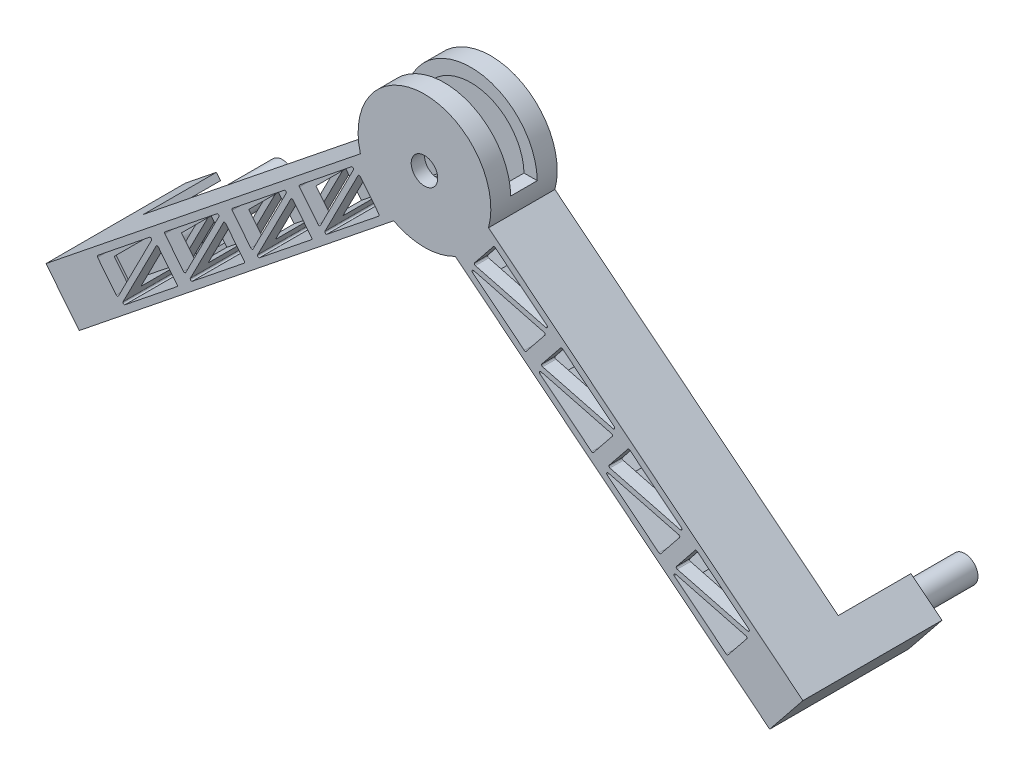
SolidWorks part; units mm, degrees
other "Markup1"
sketch "Sketch10" plane through (-187.1162, -34.3281, 104.7573) normal (-0.0779, -0.0282, 0.9966) x (0.967, 0.2412, 0.0824)
other "Markup2"
sketch "Sketch11" plane through (-187.1162, -34.3281, 104.7573) normal (-0.0779, -0.0282, 0.9966) x (0.967, 0.2412, 0.0824)
material "1060 Alloy"
ref_plane "Front Plane" through (0, 0, 0) normal (0, 0, 1) x (1, 0, 0)
ref_plane "Top Plane" through (0, 0, 0) normal (0, 1, 0) x (1, 0, 0)
ref_plane "Right Plane" through (0, 0, 0) normal (1, 0, 0) x (0, 0, -1)
sketch "Sketch1" plane through (0, 0, 0) normal (0, 0, 1) x (1, 0, 0)
  line L0 (-187.1162, 0) -> (375.3401, 0) construction
  line L1 (-187.1162, 0) -> (45.8528, 186.9213)
  line L2 (142.3711, 186.9213) -> (375.3401, 0)
  line L3 (-187.1162, 0) -> (-162.0839, -31.199)
  line L4 (-162.0839, -31.199) -> (70.8851, 155.7223)
  line L5 (117.3388, 155.7223) -> (350.3077, -31.199)
  line L6 (350.3077, -31.199) -> (375.3401, 0)
  arc A0 (70.8851, 155.7223) -> (117.3388, 155.7223) centre (94.1119, 200) ccw
  arc A1 (142.3711, 186.9213) -> (45.8528, 186.9213) centre (94.1119, 200) ccw
  dimension "D4" = 100
  dimension "D1" = 200
  dimension "D3" = 40
extrude "Boss-Extrude1" add sketch "Sketch1" along normal blind 50
shell "Shell1" thickness 10
sketch "Sketch2" plane through (0, 0, 50) normal (0, 0, 1) x (1, 0, 0)
  circle A0 centre (94.1119, 200) radius 10
  dimension "D1" = 20
extrude "Cut-Extrude1" cut sketch "Sketch2" against normal blind 50
ref_plane "Plane1" through (0, 251, 0) normal (0, 1, 0) x (1, 0, 0)
sketch "Sketch5" plane through (0, 251, 0) normal (0, 1, 0) x (1, 0, 0)
  line L0 (44.1119, 0) -> (44.1119, -50) construction
  line L1 (44.1119, -15) -> (144.1119, -15)
  line L2 (44.1119, -15) -> (44.1119, -35)
  line L3 (44.1119, -35) -> (144.1119, -35)
  line L4 (144.1119, -15) -> (144.1119, -35)
  line L5 (144.1119, -50) -> (144.1119, 0) construction
  line L6 (144.1119, 0) -> (44.1119, 0) construction
  dimension "D1" = 20
  dimension "D2" = 15
extrude "Cut-Extrude2" cut sketch "Sketch5" against normal blind 50
sketch "Sketch6" plane through (228.3429, -183.2096, 0) normal (0.78, -0.6258, 0) x (0, 0, -1)
  line L0 (-50, 234.8913) -> (0, 234.8913) construction
  line L1 (-40, 224.8913) -> (-10, 224.8913)
  line L2 (-40, 224.8913) -> (-40, 204.8913)
  line L3 (-40, 204.8913) -> (-10, 204.8913)
  line L4 (-10, 224.8913) -> (-10, 204.8913)
  line L5 (-50, 194.8913) -> (0, 194.8913) construction
  line L6 (0, 194.8913) -> (0, 234.8913) construction
  line L7 (-50, 194.8913) -> (-50, 234.8913) construction
  dimension "D1" = 10
  dimension "D2" = 10
  dimension "D3" = 10
  dimension "D4" = 10
extrude "Cut-Extrude3" cut sketch "Sketch6" against normal blind 50
sketch "Sketch7" plane through (228.3429, -183.2096, 0) normal (0.78, -0.6258, 0) x (0, 0, -1)
  line L0 (-50, 194.8913) -> (0, 194.8913) construction
  line L1 (0, 234.8913) -> (-4.7573, 234.8913)
  line L2 (0, 234.8913) -> (0, 194.8913)
  line L3 (0, 194.8913) -> (-4.7573, 194.8913)
  line L4 (-4.7573, 234.8913) -> (-4.7573, 194.8913)
extrude "Boss-Extrude2" add sketch "Sketch7" along normal blind 5
sketch "Sketch8" plane through (0, 0, 4.7573) normal (0, 0, 1) x (1, 0, 0)
  line L4 (375.3401, 0) -> (350.3077, -31.199)
  line L5 (350.3077, -31.199) -> (354.2076, -34.3281)
  line L6 (354.2076, -34.3281) -> (379.24, -3.129)
  line L7 (379.24, -3.129) -> (375.3401, 0)
  line L8 (375.3401, 0) -> (350.3077, -31.199)
  line L9 (350.3077, -31.199) -> (354.2076, -34.3281)
  line L10 (354.2076, -34.3281) -> (379.24, -3.129)
  line L11 (379.24, -3.129) -> (375.3401, 0)
  dimension "D1" = 0
extrude "Boss-Extrude3" add sketch "Sketch8" along normal blind 100
sketch "Sketch9" plane through (0, 0, 50) normal (0, 0, 1) x (1, 0, 0)
  line L0 (375.3401, 0) -> (355.8407, 15.6452)
  line L1 (375.3401, 0) -> (142.3711, 186.9213) construction
  line L2 (355.8407, 15.6452) -> (352.7117, 11.7454)
  line L3 (352.7117, 11.7454) -> (372.2111, -3.8999)
  line L4 (375.3401, 0) -> (350.3077, -31.199) construction
  line L5 (372.2111, -3.8999) -> (375.3401, 0)
  line L6 (350.3077, -31.199) -> (330.8083, -15.5538)
  line L7 (117.3388, 155.7223) -> (350.3077, -31.199) construction
  line L8 (330.8083, -15.5538) -> (333.9374, -11.6539)
  line L9 (333.9374, -11.6539) -> (353.4368, -27.2992)
  line L10 (350.3077, -31.199) -> (375.3401, 0) construction
  line L11 (353.4368, -27.2992) -> (350.3077, -31.199)
  dimension "D1" = 5
  dimension "D2" = 25
extrude "Boss-Extrude4" add sketch "Sketch9" along normal up to surface (54.7573 mm away) up to face at (364.7739, -17.164, 104.7573)
sketch "Sketch12" plane through (-113.8345, -91.3345, 0) normal (-0.78, -0.6258, 0) x (0, 0, 1)
  line L0 (50, 77.0991) -> (0, 77.0991) construction
  line L1 (0, 117.0991) -> (9.973, 117.0991)
  line L2 (0, 117.0991) -> (0, 77.0991)
  line L3 (0, 77.0991) -> (9.973, 77.0991)
  line L4 (9.973, 117.0991) -> (9.973, 77.0991)
extrude "Boss-Extrude5" add sketch "Sketch12" along normal blind 5
sketch "Sketch13" plane through (0, 0, 9.973) normal (0, 0, 1) x (1, 0, 0)
  line L4 (-162.0839, -31.199) -> (-187.1162, 0)
  line L5 (-187.1162, 0) -> (-191.0161, -3.129)
  line L6 (-191.0161, -3.129) -> (-165.9837, -34.3281)
  line L7 (-165.9837, -34.3281) -> (-162.0839, -31.199)
  line L8 (-162.0839, -31.199) -> (-187.1162, 0)
  line L9 (-187.1162, 0) -> (-191.0161, -3.129)
  line L10 (-191.0161, -3.129) -> (-165.9837, -34.3281)
  line L11 (-165.9837, -34.3281) -> (-162.0839, -31.199)
  dimension "D1" = 0
extrude "Boss-Extrude6" add sketch "Sketch13" along normal blind 95
sketch "Sketch14" plane through (0, 0, 50) normal (0, 0, 1) x (1, 0, 0)
  line L0 (-187.1162, 0) -> (-167.6168, 15.6452)
  line L1 (45.8528, 186.9213) -> (-187.1162, 0) construction
  line L2 (-167.6168, 15.6452) -> (-164.4878, 11.7454)
  line L3 (-164.4878, 11.7454) -> (-183.9872, -3.8999)
  line L4 (-187.1162, 0) -> (-162.0839, -31.199) construction
  line L5 (-183.9872, -3.8999) -> (-187.1162, 0)
  line L6 (-162.0839, -31.199) -> (-165.2129, -27.2992)
  line L7 (-165.2129, -27.2992) -> (-145.7135, -11.6539)
  line L8 (-145.7135, -11.6539) -> (-142.5845, -15.5538)
  line L9 (-162.0839, -31.199) -> (70.8851, 155.7223) construction
  line L10 (-142.5845, -15.5538) -> (-162.0839, -31.199)
  dimension "D1" = 5
  dimension "D2" = 25
extrude "Boss-Extrude7" add sketch "Sketch14" along normal up to surface (54.973 mm away) up to face at (-176.55, -17.164, 104.973)
sketch "Sketch15" plane through (0, 0, 50) normal (0, 0, 1) x (1, 0, 0)
  line L0 (-152.1623, 20.3525) -> (-138.11, 2.8384)
  line L1 (-136.4396, 3.0091) -> (-111.4931, 51.8137)
  line L2 (-113.0094, 53.0488) -> (-152.0082, 21.7583)
  line L3 (-106.341, 50.0074) -> (-92.2886, 32.4933)
  line L4 (-92.4428, 31.0875) -> (-131.4416, -0.2029)
  line L5 (-132.9578, 1.0322) -> (-108.0114, 49.8368)
  line L6 (45.8528, 186.9213) -> (-167.6168, 15.6452) construction
  line L7 (-142.5845, -15.5538) -> (70.8851, 155.7223) construction
  line L8 (-183.9872, -3.8999) -> (-165.2129, -27.2992) construction
  line L9 (-62.3109, 93.7264) -> (-101.3097, 62.4359)
  line L10 (-101.4639, 61.0301) -> (-87.4115, 43.516)
  line L11 (-85.7411, 43.6867) -> (-60.7947, 92.4913)
  line L12 (-82.2594, 41.7098) -> (-57.3129, 90.5144)
  line L13 (-55.6425, 90.6851) -> (-41.5902, 73.1709)
  line L14 (-41.7443, 71.7651) -> (-80.7431, 40.4747)
  line L15 (-11.6125, 134.404) -> (-50.6113, 103.1135)
  line L16 (-50.7654, 101.7077) -> (-36.7131, 84.1936)
  line L17 (-35.0427, 84.3643) -> (-10.0962, 133.1689)
  line L18 (-31.5609, 82.3874) -> (-6.6145, 131.192)
  line L19 (-4.9441, 131.3627) -> (9.1083, 113.8485)
  line L20 (8.9541, 112.4428) -> (-30.0447, 81.1523)
  line L21 (39.086, 175.0816) -> (0.0872, 143.7911)
  line L22 (-0.067, 142.3853) -> (13.9854, 124.8712)
  line L23 (15.6558, 125.0419) -> (40.6022, 173.8465)
  line L24 (19.1375, 123.065) -> (44.084, 171.8696)
  line L25 (45.7544, 172.0403) -> (59.8067, 154.5261)
  line L26 (59.6526, 153.1204) -> (20.6538, 121.8299)
  line L27 (322.8636, -1.4868) -> (336.9159, 16.0273)
  line L28 (336.3873, 17.621) -> (283.3361, 31.3974)
  line L29 (282.459, 29.6495) -> (321.4578, -1.641)
  line L30 (338.4397, 23.1964) -> (299.4409, 54.4868)
  line L31 (298.0352, 54.3327) -> (283.9828, 36.8185)
  line L32 (284.5114, 35.2248) -> (337.5626, 21.4485)
  line L33 (117.3388, 155.7223) -> (330.8083, -15.5538) construction
  line L34 (355.8407, 15.6452) -> (142.3711, 186.9213) construction
  line L35 (353.4368, -27.2992) -> (372.2111, -3.8999) construction
  line L36 (233.8146, 75.9011) -> (286.8658, 62.1248)
  line L37 (287.7429, 63.8727) -> (248.7441, 95.1631)
  line L38 (247.3383, 95.009) -> (233.286, 77.4948)
  line L39 (231.7622, 70.3258) -> (270.761, 39.0353)
  line L40 (272.1667, 39.1895) -> (286.2191, 56.7036)
  line L41 (285.6905, 58.2973) -> (232.6393, 72.0737)
  line L42 (183.1178, 116.5774) -> (236.169, 102.8011)
  line L43 (237.0461, 104.5489) -> (198.0473, 135.8394)
  line L44 (196.6415, 135.6852) -> (182.5892, 118.1711)
  line L45 (181.0653, 111.0021) -> (220.0641, 79.7116)
  line L46 (221.4699, 79.8658) -> (235.5223, 97.3799)
  line L47 (234.9937, 98.9736) -> (181.9425, 112.75)
  line L48 (132.421, 157.2537) -> (185.4721, 143.4774)
  line L49 (186.3493, 145.2252) -> (147.3505, 176.5157)
  line L50 (145.9447, 176.3615) -> (131.8924, 158.8474)
  line L51 (130.3685, 151.6784) -> (169.3673, 120.3879)
  line L52 (170.7731, 120.5421) -> (184.8255, 138.0562)
  line L53 (184.2968, 139.6499) -> (131.2457, 153.4263)
  arc A0 (-152.1623, 20.3525) -> (-152.0082, 21.7583) centre (-151.3824, 20.9783) cw
  arc A1 (-136.4396, 3.0091) -> (-138.11, 2.8384) centre (-137.33, 3.4642) cw
  arc A2 (-111.4931, 51.8137) -> (-113.0094, 53.0488) centre (-112.3835, 52.2688) ccw
  arc A3 (-131.4416, -0.2029) -> (-132.9578, 1.0322) centre (-132.0674, 0.577) cw
  arc A4 (-92.4428, 31.0875) -> (-92.2886, 32.4933) centre (-93.0686, 31.8675) ccw
  arc A5 (-106.341, 50.0074) -> (-108.0114, 49.8368) centre (-107.1209, 49.3816) ccw
  arc A6 (-60.7947, 92.4913) -> (-62.3109, 93.7264) centre (-61.6851, 92.9464) ccw
  arc A7 (-101.4639, 61.0301) -> (-101.3097, 62.4359) centre (-100.6839, 61.6559) cw
  arc A8 (-85.7411, 43.6867) -> (-87.4115, 43.516) centre (-86.6316, 44.1418) cw
  arc A9 (-55.6425, 90.6851) -> (-57.3129, 90.5144) centre (-56.4225, 90.0592) ccw
  arc A10 (-80.7431, 40.4747) -> (-82.2594, 41.7098) centre (-81.3689, 41.2547) cw
  arc A11 (-41.7443, 71.7651) -> (-41.5902, 73.1709) centre (-42.3701, 72.5451) ccw
  arc A12 (-10.0962, 133.1689) -> (-11.6125, 134.404) centre (-10.9867, 133.624) ccw
  arc A13 (-50.7654, 101.7077) -> (-50.6113, 103.1135) centre (-49.9855, 102.3335) cw
  arc A14 (-35.0427, 84.3643) -> (-36.7131, 84.1936) centre (-35.9331, 84.8194) cw
  arc A15 (-4.9441, 131.3627) -> (-6.6145, 131.192) centre (-5.724, 130.7369) ccw
  arc A16 (-30.0447, 81.1523) -> (-31.5609, 82.3874) centre (-30.6705, 81.9323) cw
  arc A17 (8.9541, 112.4428) -> (9.1083, 113.8485) centre (8.3283, 113.2227) ccw
  arc A18 (40.6022, 173.8465) -> (39.086, 175.0816) centre (39.7118, 174.3016) ccw
  arc A19 (-0.067, 142.3853) -> (0.0872, 143.7911) centre (0.713, 143.0111) cw
  arc A20 (15.6558, 125.0419) -> (13.9854, 124.8712) centre (14.7653, 125.497) cw
  arc A21 (45.7544, 172.0403) -> (44.084, 171.8696) centre (44.9744, 171.4145) ccw
  arc A22 (20.6538, 121.8299) -> (19.1375, 123.065) centre (20.028, 122.6099) cw
  arc A23 (59.6526, 153.1204) -> (59.8067, 154.5261) centre (59.0268, 153.9003) ccw
  arc A24 (336.9159, 16.0273) -> (336.3873, 17.621) centre (336.1359, 16.6531) ccw
  arc A25 (322.8636, -1.4868) -> (321.4578, -1.641) centre (322.0836, -0.861) cw
  arc A26 (282.459, 29.6495) -> (283.3361, 31.3974) centre (283.0848, 30.4295) cw
  arc A27 (337.5626, 21.4485) -> (338.4397, 23.1964) centre (337.8139, 22.4164) ccw
  arc A28 (284.5114, 35.2248) -> (283.9828, 36.8185) centre (284.7628, 36.1927) cw
  arc A29 (299.4409, 54.4868) -> (298.0352, 54.3327) centre (298.8151, 53.7068) ccw
  arc A30 (233.8146, 75.9011) -> (233.286, 77.4948) centre (234.066, 76.869) cw
  arc A31 (286.8658, 62.1248) -> (287.7429, 63.8727) centre (287.1171, 63.0927) ccw
  arc A32 (248.7441, 95.1631) -> (247.3383, 95.009) centre (248.1183, 94.3831) ccw
  arc A33 (231.7622, 70.3258) -> (232.6393, 72.0737) centre (232.388, 71.1058) cw
  arc A34 (272.1667, 39.1895) -> (270.761, 39.0353) centre (271.3868, 39.8153) cw
  arc A35 (286.2191, 56.7036) -> (285.6905, 58.2973) centre (285.4391, 57.3294) ccw
  arc A36 (183.1178, 116.5774) -> (182.5892, 118.1711) centre (183.3691, 117.5453) cw
  arc A37 (236.169, 102.8011) -> (237.0461, 104.5489) centre (236.4203, 103.769) ccw
  arc A38 (198.0473, 135.8394) -> (196.6415, 135.6852) centre (197.4215, 135.0594) ccw
  arc A39 (181.0653, 111.0021) -> (181.9425, 112.75) centre (181.6912, 111.7821) cw
  arc A40 (221.4699, 79.8658) -> (220.0641, 79.7116) centre (220.69, 80.4916) cw
  arc A41 (235.5223, 97.3799) -> (234.9937, 98.9736) centre (234.7423, 98.0057) ccw
  arc A42 (132.421, 157.2537) -> (131.8924, 158.8474) centre (132.6723, 158.2216) cw
  arc A43 (185.4721, 143.4774) -> (186.3493, 145.2252) centre (185.7235, 144.4453) ccw
  arc A44 (147.3505, 176.5157) -> (145.9447, 176.3615) centre (146.7247, 175.7357) ccw
  arc A45 (130.3685, 151.6784) -> (131.2457, 153.4263) centre (130.9943, 152.4584) cw
  arc A46 (170.7731, 120.5421) -> (169.3673, 120.3879) centre (169.9931, 121.1679) cw
  arc A47 (184.8255, 138.0562) -> (184.2968, 139.6499) centre (184.0455, 138.682) ccw
  point P12 (-152.7881, 21.1325)
  point P15 (-137.1429, 1.6331)
  point P22 (-91.6628, 31.7133)
  point P25 (-107.308, 51.2128)
  point P97 (337.883, 17.2326)
  point P100 (322.2378, -2.2668)
  point P103 (278.8183, 32.5705)
  dimension "D5" = 1
  dimension "D6" = 1
  dimension "D17" = 1
  dimension "D1" = 5
  dimension "D2" = 5
  dimension "D3" = 25
  dimension "D4" = 25
  dimension "D7" = 50
  dimension "D8" = 4
  dimension "D9" = 40
  dimension "D11" = 25
  dimension "D12" = 50
  dimension "D13" = 5
  dimension "D14" = 4
  dimension "D15" = 5
  dimension "D16" = 40
  dimension "D19" = 10.7
  dimension "D10" = 4
  dimension "D18" = 4
extrude "Cut-Extrude4" cut sketch "Sketch15" against normal blind 95
sketch "Sketch16" plane through (0, 0, 50) normal (0, 0, 1) x (1, 0, 0)
  line L2 (-183.9872, -3.8999) -> (-164.4878, 11.7454) construction
  line L4 (-183.9872, -3.8999) -> (-165.2129, -27.2992) construction
  circle A0 centre (-162.9004, -6.2124) radius 10
  dimension "D1" = 20
  dimension "D2" = 15
  dimension "D3" = 15
extrude "Boss-Extrude8" add sketch "Sketch16" along normal blind 100
sketch "Sketch18" plane through (0, 0, 50) normal (0, 0, 1) x (1, 0, 0)
  line L0 (353.4368, -27.2992) -> (333.9374, -11.6539) construction
  line L1 (372.2111, -3.8999) -> (353.4368, -27.2992) construction
  circle A0 centre (351.1243, -6.2124) radius 10
  dimension "D1" = 20
  dimension "D2" = 15
  dimension "D3" = 15
extrude "Boss-Extrude9" add sketch "Sketch18" along normal blind 100
mirror "Mirror2" about plane through (0, 0, 0) normal (0, 0, 1) of bodies 113
delete or keep bodies "Body-Delete/Keep 1" type delete bodies bodies 113
